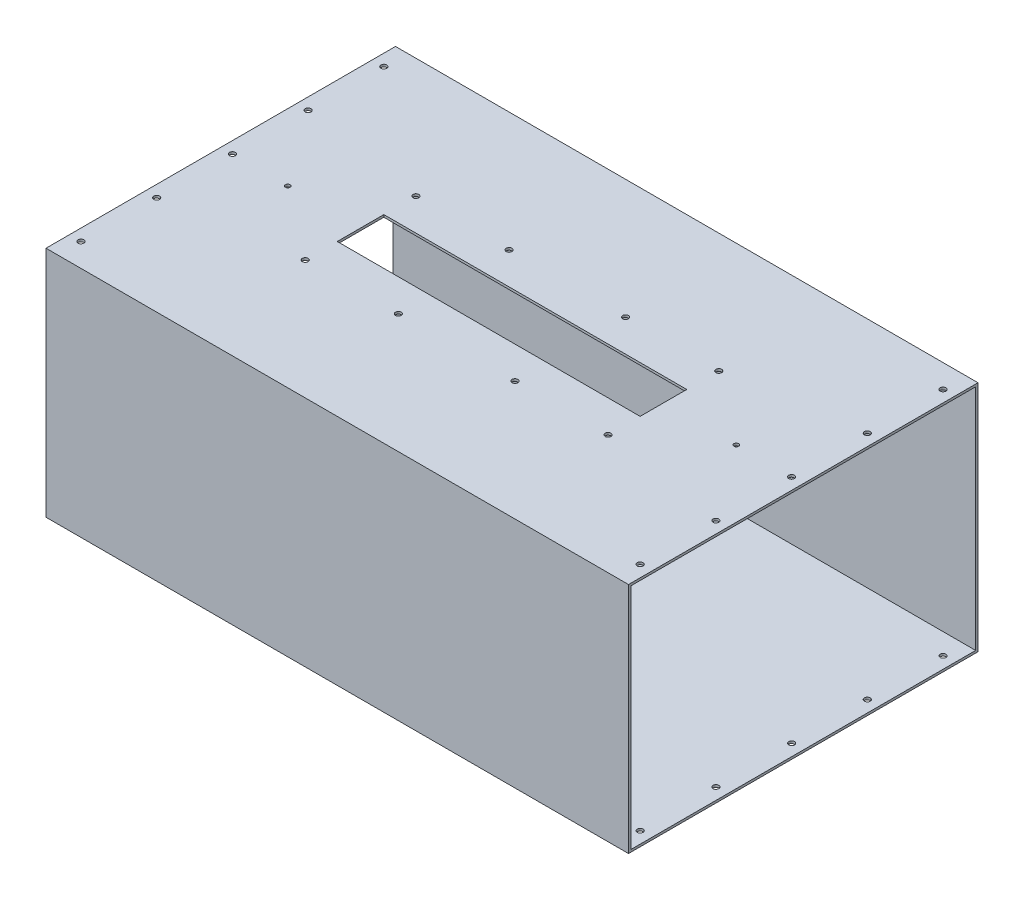
SolidWorks part; units mm, degrees
ref_plane "Plano frontal" through (0, 0, 0) normal (0, 0, 1) x (1, 0, 0)
ref_plane "Plano superior" through (0, 0, 0) normal (0, 1, 0) x (1, 0, 0)
ref_plane "Plano direito" through (0, 0, 0) normal (1, 0, 0) x (0, 0, -1)
sketch "Esboço1" plane through (0, 0, 0) normal (1, 0, 0) x (0, 0, -1)
  line L1 (150, -100) -> (-150, -100)
  line L2 (150, -100) -> (150, 100)
  line L3 (150, 100) -> (-150, 100)
  line L4 (-150, -100) -> (-150, 100)
  line L5 (150, -100) -> (-150, 100) construction
  line L6 (150, 100) -> (-150, -100) construction
  point P0 (0, 0)
  dimension "D1" = 200
  dimension "D2" = 300
extrude "Ressalto-extrusão1" add sketch "Esboço1" along normal blind 500
sketch "Esboço2" plane through (500, 0, 0) normal (1, 0, 0) x (0, 0, -1)
  line L0 (-150, 100) -> (-150, -100) construction
  line L1 (148, -98) -> (-148, -98)
  line L2 (148, -98) -> (148, 98)
  line L3 (148, 98) -> (-148, 98)
  line L4 (-148, -98) -> (-148, 98)
  line L5 (148, -98) -> (-148, 98) construction
  line L6 (148, 98) -> (-148, -98) construction
  line L7 (-150, -100) -> (150, -100) construction
  point P0 (0, 0)
  dimension "D1" = 2
  dimension "D2" = 2
extrude "Corte-extrusão1" cut sketch "Esboço2" against normal through all
sketch "Esboço3" plane through (0, 100, 0) normal (0, 1, 0) x (1, 0, 0)
  line L0 (-55.7829, 0) -> (555.7829, 0) construction
  line L1 (250, 178.9199) -> (250, -196.7096) construction
  line L2 (380, -20) -> (120, -20)
  line L3 (380, -20) -> (380, 20)
  line L4 (380, 20) -> (120, 20)
  line L5 (120, -20) -> (120, 20)
  line L6 (380, -20) -> (120, 20) construction
  line L7 (380, 20) -> (120, -20) construction
  line L8 (39.5274, 47.5) -> (464.079, 47.5) construction
  circle A0 centre (57.5, 0) radius 2
  circle A1 centre (442.5, 0) radius 2
  circle A2 centre (120, 47.5) radius 2.5
  circle A3 centre (200, 47.5) radius 2.5
  circle A4 centre (300, 47.5) radius 2.5
  circle A5 centre (380, 47.5) radius 2.5
  circle A6 centre (380, -47.5) radius 2.5
  circle A7 centre (300, -47.5) radius 2.5
  circle A8 centre (200, -47.5) radius 2.5
  circle A9 centre (120, -47.5) radius 2.5
  point P3 (250, 0)
  dimension "D3" = 4
  dimension "D4" = 192.5
  dimension "D6" = 5
  dimension "D7" = 50
  dimension "D8" = 80
  dimension "D1" = 260
  dimension "D2" = 40
  dimension "D5" = 47.5
extrude "Corte-extrusão2" cut sketch "Esboço3" against normal blind 10
sketch "Esboço5" plane through (0, 100, 0) normal (0, 1, 0) x (1, 0, 0)
  line L0 (250, 174.196) -> (250, -190.9054) construction
  line L1 (-27.3768, 0) -> (517.3512, 0) construction
  line L2 (490, 168.3477) -> (490, -173.3605) construction
  line L3 (500, 150) -> (500, -150) construction
  line L4 (500, 150) -> (0, 150) construction
  circle A0 centre (490, 130) radius 2.5
  circle A1 centre (490, 65) radius 2.5
  circle A2 centre (490, 0) radius 2.5
  circle A3 centre (490, -65) radius 2.5
  circle A4 centre (490, -130) radius 2.5
  circle A5 centre (10, -130) radius 2.5
  circle A6 centre (10, -65) radius 2.5
  circle A7 centre (10, 0) radius 2.5
  circle A8 centre (10, 65) radius 2.5
  circle A9 centre (10, 130) radius 2.5
  dimension "D2" = 5
  dimension "D3" = 20
  dimension "D4" = 65
  dimension "D1" = 10
extrude "Corte-extrusão3" cut sketch "Esboço5" against normal through all
